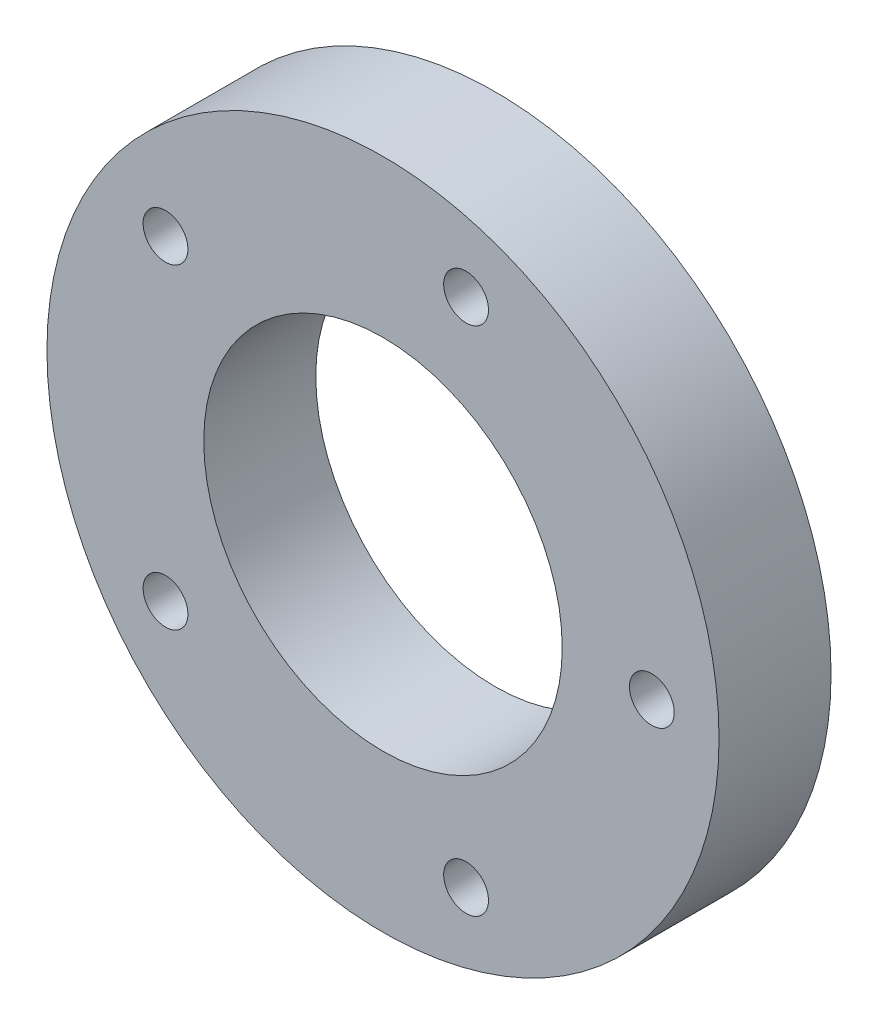
SolidWorks part; units mm, degrees
material "PET"
ref_plane "Front Plane" through (0, 0, 0) normal (0, 0, 1) x (1, 0, 0)
ref_plane "Top Plane" through (0, 0, 0) normal (0, 1, 0) x (1, 0, 0)
ref_plane "Right Plane" through (0, 0, 0) normal (1, 0, 0) x (0, 0, -1)
sketch "Sketch1" plane through (0, 0, 0) normal (0, 0, 1) x (1, 0, 0)
  line L0 (0, 0) -> (24, 0) construction
  circle A0 centre (0, 0) radius 30
  circle A1 centre (0, 0) radius 16
  circle A2 centre (24, 0) radius 2
  circle A3 centre (7.4164, -22.8254) radius 2
  circle A4 centre (-19.4164, -14.1068) radius 2
  circle A5 centre (-19.4164, 14.1068) radius 2
  circle A6 centre (7.4164, 22.8254) radius 2
  point P16 (0, 0)
  dimension "D1" = 32
  dimension "D2" = 60
  dimension "D3" = 4
  dimension "D4" = 24
  dimension "D5" = 5
extrude "Boss-Extrude1" add sketch "Sketch1" against normal blind 10
